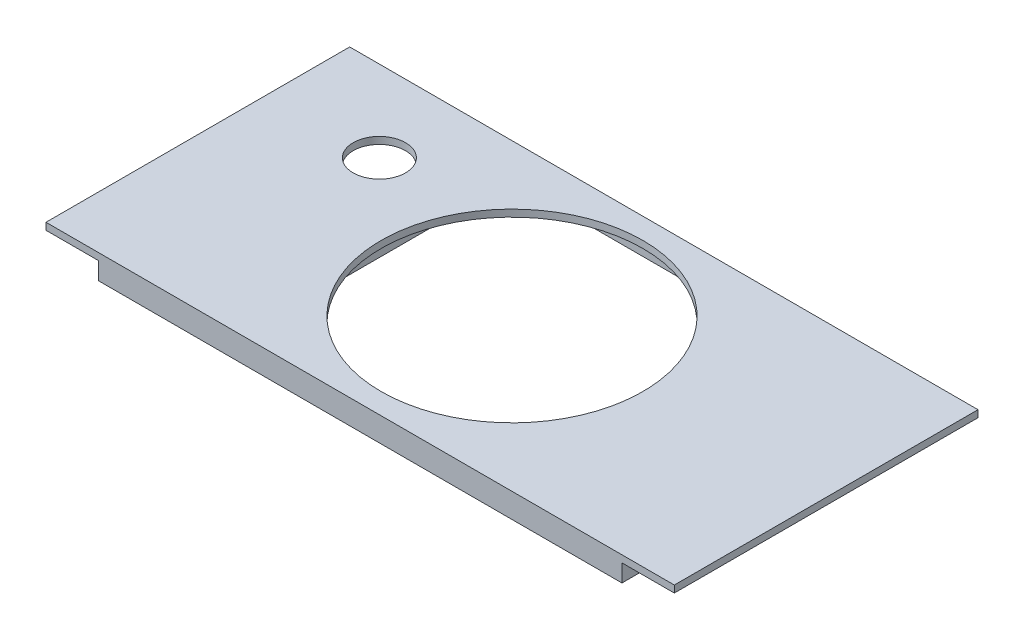
SolidWorks part; units mm, degrees
ref_plane "Front Plane" through (0, 0, 0) normal (0, 0, 1) x (1, 0, 0)
ref_plane "Top Plane" through (0, 0, 0) normal (0, 1, 0) x (1, 0, 0)
ref_plane "Right Plane" through (0, 0, 0) normal (1, 0, 0) x (0, 0, -1)
sketch "Sketch1" plane through (0, 0, 0) normal (0, 1, 0) x (1, 0, 0)
  line L1 (-58.403, 46.2981) -> (121.597, 46.2981)
  line L2 (-58.403, 46.2981) -> (-58.403, -40.7019)
  line L3 (-58.403, -40.7019) -> (121.597, -40.7019)
  line L4 (121.597, 46.2981) -> (121.597, -40.7019)
  dimension "D1" = 180
  dimension "D2" = 87
extrude "Boss-Extrude1" add sketch "Sketch1" along normal blind 2
sketch "Sketch6" plane through (0, 0, 0) normal (0, -1, 0) x (-1, 0, 0)
  line L0 (58.403, -40.7019) -> (-121.597, -40.7019) construction
  line L1 (45.403, -40.7019) -> (43.403, -40.7019)
  line L2 (45.403, -40.7019) -> (45.403, 46.2981)
  line L3 (45.403, 46.2981) -> (43.403, 46.2981)
  line L4 (43.403, -40.7019) -> (43.403, 46.2981)
  line L5 (-121.597, 46.2981) -> (58.403, 46.2981) construction
  line L6 (58.403, 46.2981) -> (58.403, -40.7019) construction
  line L7 (-106.597, -40.7019) -> (-108.597, -40.7019)
  line L8 (-106.597, -40.7019) -> (-106.597, 46.2981)
  line L9 (-106.597, 46.2981) -> (-108.597, 46.2981)
  line L10 (-108.597, -40.7019) -> (-108.597, 46.2981)
  line L11 (-121.597, -40.7019) -> (-121.597, 46.2981) construction
  dimension "D1" = 2
  dimension "D2" = 2
  dimension "D3" = 15
  dimension "D4" = 15
extrude "Boss-Extrude5" add sketch "Sketch6" along normal blind 5
sketch "Sketch7" plane through (0, 0, 0) normal (0, -1, 0) x (-1, 0, 0)
  line L0 (-31.597, -40.7019) -> (-31.597, 46.2981) construction
  line L1 (43.403, -40.7019) -> (-106.597, -40.7019) construction
  line L2 (-106.597, 46.2981) -> (43.403, 46.2981) construction
  line L3 (43.403, 2.7981) -> (-106.597, 2.7981) construction
  line L4 (43.403, 46.2981) -> (43.403, -40.7019) construction
  line L5 (-106.597, -40.7019) -> (-106.597, 46.2981) construction
  circle A0 centre (-31.597, 2.7981) radius 37.5
  dimension "D1" = 75
extrude "Cut-Extrude2" cut sketch "Sketch7" against normal blind 5
sketch "Sketch8" plane through (0, 0, 0) normal (0, -1, 0) x (-1, 0, 0)
  line L0 (43.403, -40.7019) -> (-106.597, -40.7019) construction
  line L1 (8.903, 43.2981) -> (-72.097, 43.2981)
  line L2 (8.903, 43.2981) -> (8.903, -37.7019)
  line L3 (8.903, -37.7019) -> (-72.097, -37.7019)
  line L4 (-72.097, 43.2981) -> (-72.097, -37.7019)
  line L5 (8.903, 43.2981) -> (-72.097, -37.7019) construction
  line L6 (8.903, -37.7019) -> (-72.097, 43.2981) construction
  line L7 (11.903, 46.2981) -> (-75.097, 46.2981)
  line L8 (11.903, 46.2981) -> (11.903, -40.7019)
  line L9 (11.903, -40.7019) -> (-75.097, -40.7019)
  line L10 (-75.097, 46.2981) -> (-75.097, -40.7019)
  line L11 (11.903, 46.2981) -> (-75.097, -40.7019) construction
  line L12 (11.903, -40.7019) -> (-75.097, 46.2981) construction
  point P0 (-31.597, 2.7981)
  point P6 (-31.597, 2.7981)
  dimension "D1" = 81
  dimension "D2" = 81
  dimension "D3" = 3
extrude "Boss-Extrude6" add sketch "Sketch8" along normal blind 5
sketch "Sketch9" plane through (0, 0, 0) normal (0, -1, 0) x (-1, 0, 0)
  line L0 (43.403, 46.2981) -> (43.403, -40.7019) construction
  line L1 (-106.597, 46.2981) -> (43.403, 46.2981)
  line L2 (-106.597, 46.2981) -> (-106.597, 43.2981)
  line L3 (-106.597, 43.2981) -> (43.403, 43.2981)
  line L4 (43.403, 46.2981) -> (43.403, 43.2981)
  line L6 (-106.597, -40.7019) -> (43.403, -40.7019)
  line L7 (-106.597, -40.7019) -> (-106.597, -37.7019)
  line L8 (-106.597, -37.7019) -> (43.403, -37.7019)
  line L9 (43.403, -40.7019) -> (43.403, -37.7019)
  dimension "D1" = 3
  dimension "D2" = 3
extrude "Boss-Extrude7" add sketch "Sketch9" along normal blind 5
sketch "Sketch10" plane through (0, -5, 0) normal (0, -1, 0) x (-1, 0, 0)
  line L0 (-108.597, -40.7019) -> (45.403, -40.7019) construction
  line L1 (-108.597, 46.2981) -> (-106.597, 46.2981)
  line L2 (-108.597, 46.2981) -> (-108.597, -40.7019)
  line L3 (-108.597, -40.7019) -> (-106.597, -40.7019)
  line L4 (-106.597, 46.2981) -> (-106.597, -40.7019)
  line L5 (45.403, 46.2981) -> (-108.597, 46.2981) construction
  line L6 (45.403, -40.7019) -> (43.403, -40.7019)
  line L7 (45.403, -40.7019) -> (45.403, 46.2981)
  line L8 (45.403, 46.2981) -> (43.403, 46.2981)
  line L9 (43.403, -40.7019) -> (43.403, 46.2981)
extrude "Cut-Extrude3" cut sketch "Sketch10" against normal up to surface (5 mm away) up to face at (-51.903, 0, 8.0769)
sketch "Sketch11" plane through (0, 0, 0) normal (0, -1, 0) x (-1, 0, 0)
  line L0 (43.403, -37.7019) -> (11.903, -37.7019) construction
  line L1 (43.403, 43.2981) -> (41.403, 43.2981)
  line L2 (43.403, 43.2981) -> (43.403, -37.7019)
  line L3 (43.403, -37.7019) -> (41.403, -37.7019)
  line L4 (41.403, 43.2981) -> (41.403, -37.7019)
  line L5 (-106.597, 43.2981) -> (-75.097, 43.2981) construction
  line L6 (-106.597, -37.7019) -> (-104.597, -37.7019)
  line L7 (-106.597, -37.7019) -> (-106.597, 43.2981)
  line L8 (-106.597, 43.2981) -> (-104.597, 43.2981)
  line L9 (-104.597, -37.7019) -> (-104.597, 43.2981)
  dimension "D1" = 2
  dimension "D2" = 2
extrude "Boss-Extrude8" add sketch "Sketch11" along normal blind 5
sketch "Sketch12" plane through (0, 0, 0) normal (0, -1, 0) x (-1, 0, 0)
  line L0 (11.903, 2.7981) -> (41.403, 2.7981) construction
  line L1 (11.903, -37.7019) -> (11.903, 43.2981) construction
  line L2 (41.403, 43.2981) -> (41.403, -37.7019) construction
  line L3 (26.653, 2.7981) -> (26.653, 43.2981) construction
  line L4 (11.903, 43.2981) -> (41.403, 43.2981) construction
  circle A0 centre (26.653, 23.0481) radius 7.5
  dimension "D1" = 15
extrude "Cut-Extrude4" cut sketch "Sketch12" against normal blind 5
